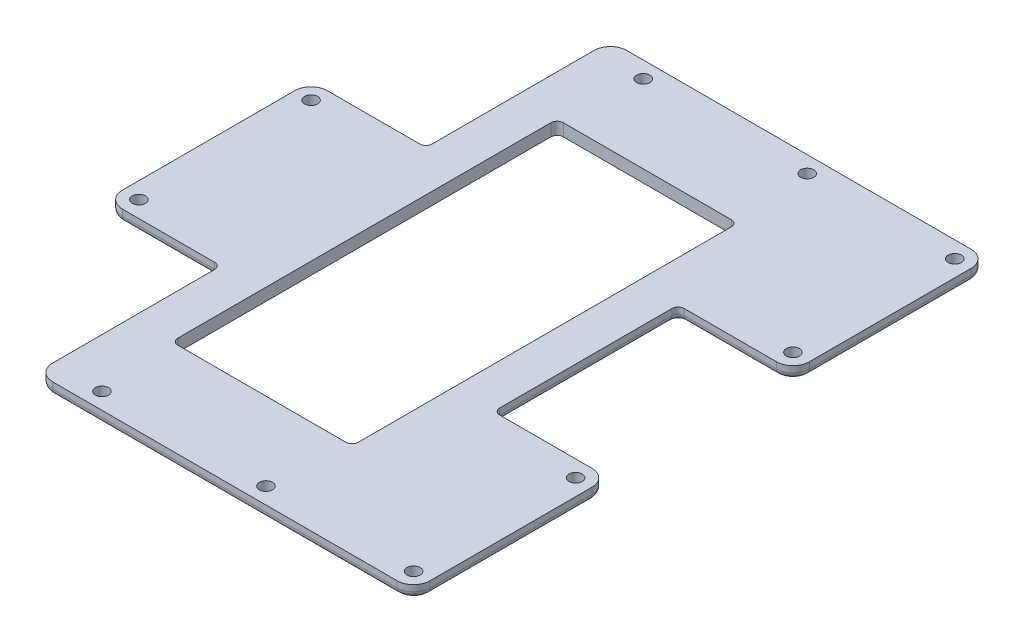
SolidWorks part; units mm, degrees
ref_plane "Front Plane" through (0, 0, 0) normal (0, 0, 1) x (1, 0, 0)
ref_plane "Top Plane" through (0, 0, 0) normal (0, 1, 0) x (1, 0, 0)
ref_plane "Right Plane" through (0, 0, 0) normal (1, 0, 0) x (0, 0, -1)
sketch "Sketch3" plane through (0, 0, 0) normal (0, 1, 0) x (1, 0, 0)
  line L0 (-22, 80) -> (-22, 35)
  line L1 (-50, -60) -> (70, -60)
  line L2 (-50, -60) -> (-50, 80)
  line L3 (-50, 80) -> (70, 80)
  line L4 (70, -60) -> (70, 80)
  line L5 (-22, 35) -> (-50, 35)
  line L6 (-50, -15) -> (-22, -15)
  line L7 (-22, -15) -> (-22, -60)
  line L8 (70, -12.5) -> (42, -12.5)
  line L9 (42, -12.5) -> (42, 32.5)
  line L10 (42, 32.5) -> (70, 32.5)
  point P0 (0, 0)
  dimension "D1" = 120
  dimension "D2" = 140
  dimension "D3" = 60
  dimension "D4" = 50
  dimension "D5" = 45
  dimension "D6" = 28
  dimension "D7" = 28
  dimension "D8" = 45
  dimension "D9" = 28
  dimension "D10" = 47.5
  dimension "D11" = 47.5
extrude "Boss-Extrude1" add sketch "Sketch3" along normal blind 3 contours L9 L10 L4 L3 L0 L5 L2 L6 L7 L1 L8
sketch "Sketch4" plane through (0, 3, 0) normal (0, 1, 0) x (1, 0, 0)
  line L1 (-12, 57) -> (32, 57)
  line L3 (-12, -37) -> (32, -37)
  line L4 (32, 57) -> (32, -37)
  line L5 (-22, 80) -> (70, 80) construction
  line L6 (-22, -60) -> (70, -60) construction
  line L7 (-12, 57) -> (-12, -37)
  line L8 (-22, 80) -> (-22, 35) construction
  dimension "D1" = 10
  dimension "D2" = 23
  dimension "D3" = 23
  dimension "D4" = 94
  dimension "D5" = 44
fillet "Fillet2" radius 4 8 edges at (70, 1.5, -32.5) (70, 1.5, -80) (-50, 1.5, -35) (-50, 1.5, 15) (-22, 1.5, 60) (70, 1.5, 12.5) (70, 1.5, 60) (-22, 1.5, -80)
sketch "Sketch7" plane through (0, 3, 0) normal (0, 1, 0) x (1, 0, 0)
  line L0 (-22, 35) -> (-46, 35) construction
  line L1 (-50, -11) -> (-50, 31) construction
  line L2 (-46, -15) -> (-22, -15) construction
  line L3 (70, -56) -> (70, -16.5) construction
  line L4 (-18, -60) -> (66, -60) construction
  line L5 (-18, 80) -> (66, 80) construction
  line L6 (70, 36.5) -> (70, 76) construction
  line L9 (-18, 80) -> (66, 80) construction
  circle A0 centre (-46, 31) radius 1.6
  circle A1 centre (-46, -11) radius 1.6
  circle A2 centre (66, -56) radius 1.6
  circle A3 centre (66, 76) radius 1.6
  circle A4 centre (-10, 76) radius 1.6
  circle A5 centre (-10, -56) radius 1.6
  circle A6 centre (30, -56) radius 1.6
  circle A7 centre (30, 76) radius 1.6
  circle A8 centre (66, -16.5) radius 1.6
  circle A9 centre (66, 36.5) radius 1.6
  dimension "D1" = 3.2
  dimension "D6" = 3.2
  dimension "D7" = 4
  dimension "D9" = 3.2
  dimension "D12" = 3.2
  dimension "D15" = 3.2
  dimension "D18" = 3.2
  dimension "D19" = 3.2
  dimension "D22" = 3.2
  dimension "D25" = 3.2
  dimension "D28" = 3.2
  dimension "D2" = 4
  dimension "D3" = 4
  dimension "D4" = 4
  dimension "D5" = 4
  dimension "D8" = 4
  dimension "D10" = 4
  dimension "D11" = 4
  dimension "D13" = 4
  dimension "D14" = 40
  dimension "D16" = 40
  dimension "D17" = 4
  dimension "D20" = 4
  dimension "D21" = 40
  dimension "D23" = 40
  dimension "D24" = 4
  dimension "D26" = 43.5
  dimension "D27" = 4
  dimension "D29" = 4
  dimension "D30" = 43.5
extrude "Cut-Extrude2" cut sketch "Sketch7" against normal through all and the other way through all
extrude "Cut-Extrude3" cut sketch "Sketch4" against normal blind 10
fillet "Fillet3" radius 1.5 28 edges at (-34, 0, -35) (-48.8284, 0, -33.8284) (-50, 0, -10) (-48.8284, 0, 13.8284) (54, 0, -32.5) (68.8284, 0, -33.6716) (70, 0, -56.25) (68.8284, 0, -78.8284) (24, 0, -80) (-20.8284, 0, -78.8284) (54, 0, 12.5) (68.8284, 0, 13.6716) (70, 0, 36.25) (68.8284, 0, 58.8284) (24, 0, 60) (-20.8284, 0, 58.8284) (42, 0, -10) (-34, 0, 15) (-22, 0, -55.5) (-22, 0, 35.5) (42, 1.5, -32.5) (42, 1.5, 12.5) (-12, 1.5, 37) (32, 1.5, 37) (32, 1.5, -57) (-12, 1.5, -57) (-22, 1.5, -35) (-22, 1.5, 15)
